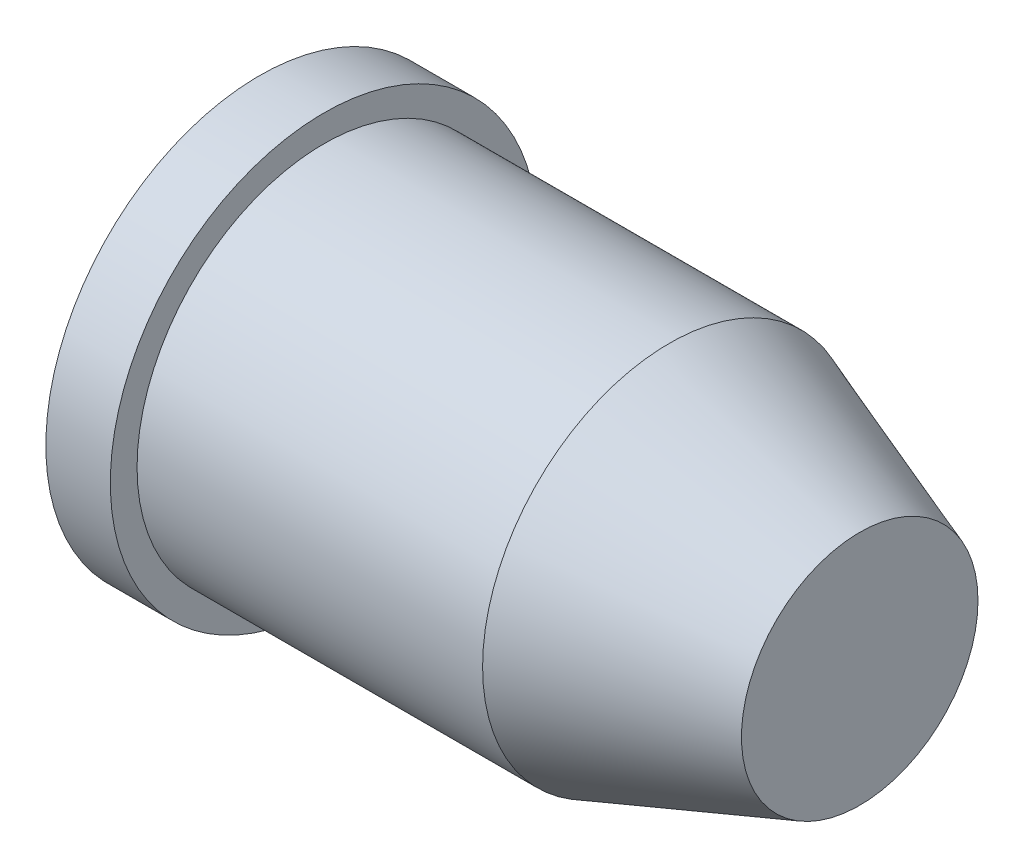
SolidWorks part; units mm, degrees
ref_plane "Front Plane" through (0, 0, 0) normal (0, 0, 1) x (1, 0, 0)
ref_plane "Top Plane" through (0, 0, 0) normal (0, 1, 0) x (1, 0, 0)
ref_plane "Right Plane" through (0, 0, 0) normal (1, 0, 0) x (0, 0, -1)
sketch "CL" plane through (0, 0, 0) normal (0, 0, 1) x (1, 0, 0)
  line L0 (113.972, 0) -> (-120.46, 0) construction
  point P3 (0, 0)
  point P4 (0, 0)
  point P5 (113.972, 0)
sketch "Sketch2" plane through (0, 0, 0) normal (0, 0, 1) x (1, 0, 0)
  line L8 (0, 63.7526) -> (0, 33.8422)
  line L9 (0, 33.8422) -> (115.532, 33.8422)
  line L10 (115.532, 33.8422) -> (160.2552, 16.1808)
  line L11 (160.2552, 16.1808) -> (160.2552, 0)
  line L12 (160.2552, 0) -> (179.1431, 0)
  line L13 (179.1431, 0) -> (179.1431, 35.2961)
  line L14 (179.1431, 35.2961) -> (122.3687, 55.7765)
  line L15 (122.3687, 55.7765) -> (19.2489, 55.7765)
  line L16 (19.2489, 55.7765) -> (19.2489, 63.7526)
  line L17 (19.2489, 63.7526) -> (0, 63.7526)
  point P3 (179.1431, 35.2961)
revolve "Revolve1" add sketch "Sketch2" angle 360 about L0
equation "\"OD\"= 100"
equation "\"ID\"= 80"
